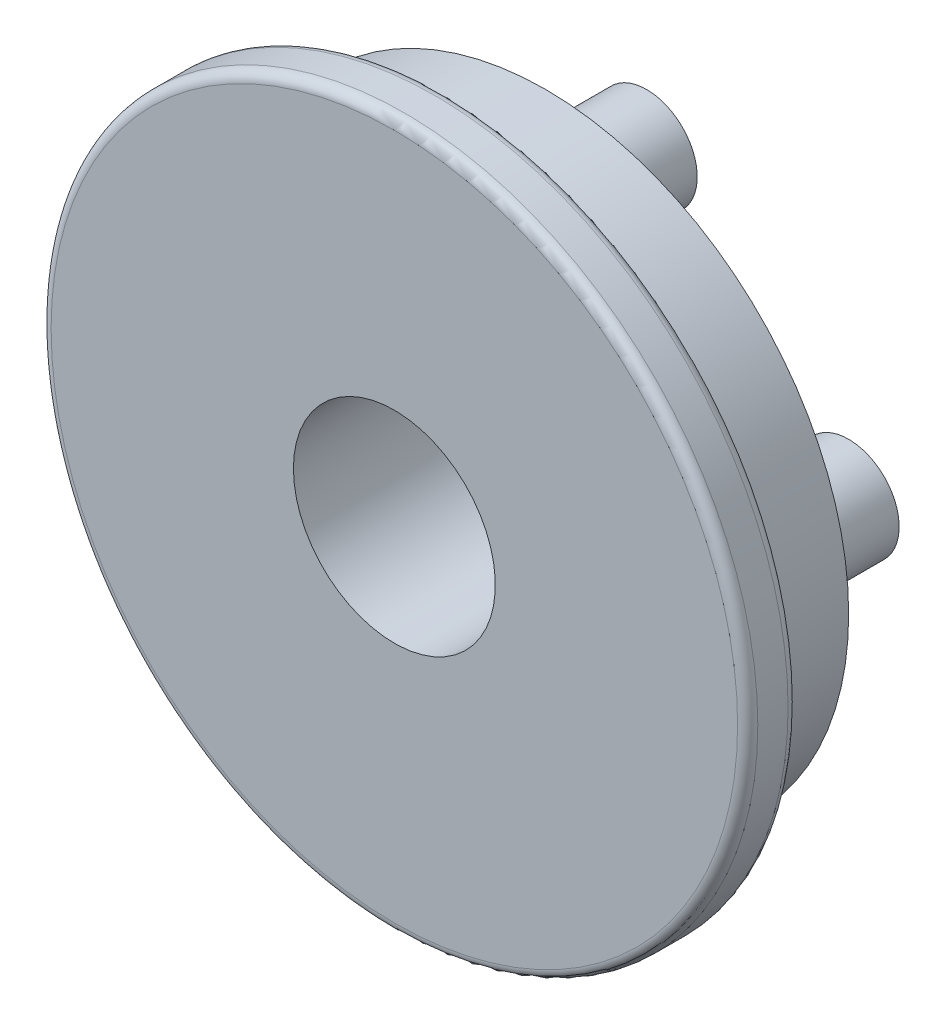
SolidWorks part; units mm, degrees
ref_plane "Front Plane" through (0, 0, 0) normal (0, 0, 1) x (1, 0, 0)
ref_plane "Top Plane" through (0, 0, 0) normal (0, 1, 0) x (1, 0, 0)
ref_plane "Right Plane" through (0, 0, 0) normal (1, 0, 0) x (0, 0, -1)
sketch "Sketch1" plane through (0, 0, 0) normal (0, 0, 1) x (1, 0, 0)
  circle A0 centre (0, 0) radius 35
extrude "Boss-Extrude1" add sketch "Sketch1" along normal blind 5
fillet "Fillet1" radius 1 2 edges at (35, 0, 0) (35, 0, 5)
sketch "Sketch2" plane through (0, 0, 0) normal (0, 0, -1) x (-1, 0, 0)
  circle A0 centre (0, 0) radius 30
extrude "Boss-Extrude2" add sketch "Sketch2" along normal blind 10
sketch "Sketch3" plane through (0, 0, -10) normal (0, 0, -1) x (-1, 0, 0)
  circle A0 centre (0, 0) radius 20 construction
  circle A1 centre (0, 20) radius 5
  circle A2 centre (20, 0) radius 5
  circle A3 centre (0, -20) radius 5
  circle A4 centre (-20, 0) radius 5
  point P14 (0, 0)
  dimension "D1" = 4
extrude "Boss-Extrude3" add sketch "Sketch3" along normal blind 10
sketch "Sketch4" plane through (0, 0, -10) normal (0, 0, -1) x (-1, 0, 0)
  circle A0 centre (0, 0) radius 10
extrude "Cut-Extrude1" cut sketch "Sketch4" against normal through all
